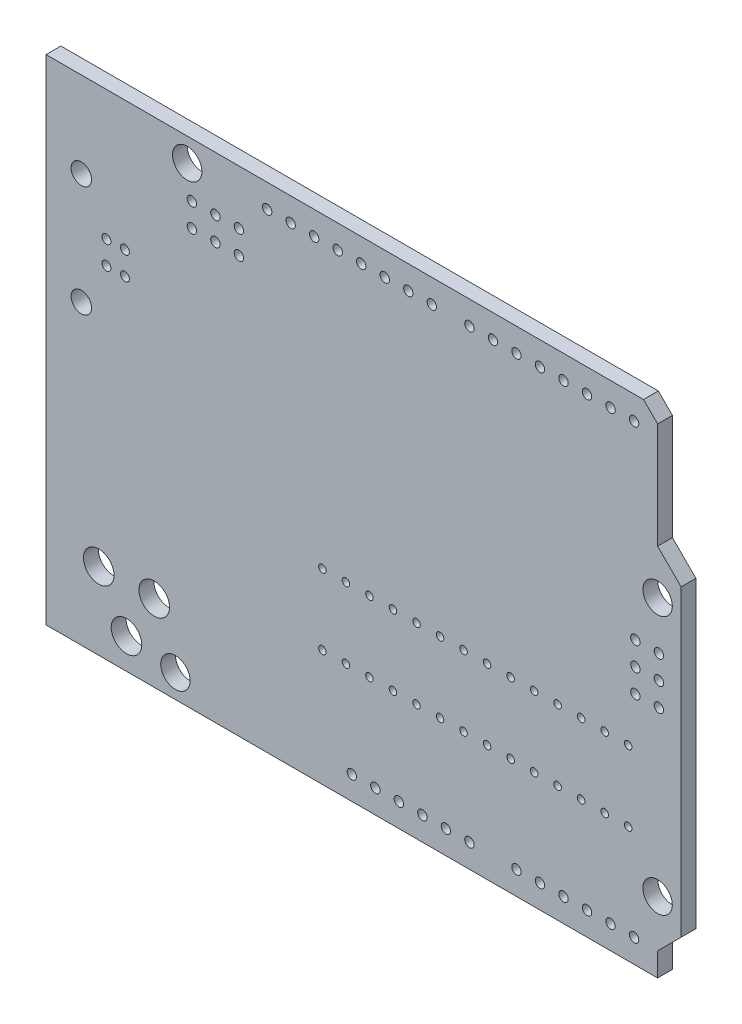
SolidWorks part; units mm, degrees
ref_plane "Front" through (0, 0, 0) normal (0, 0, 1) x (1, 0, 0)
ref_plane "Top" through (0, 0, 0) normal (0, 1, 0) x (1, 0, 0)
ref_plane "Right" through (0, 0, 0) normal (1, 0, 0) x (0, 0, -1)
sketch "Sketch1" plane through (0, 0, 0) normal (0, 0, 1) x (1, 0, 0)
  line L0 (-34.2899, 0) -> (34.2899, 0) construction
  line L1 (0, 0) -> (0, 7.605) construction
  line L2 (31.7499, 13.716) -> (31.7499, 25.146) construction
  line L3 (-34.2899, -26.67) -> (-34.2899, 26.67) construction
  line L4 (-34.2899, -26.67) -> (31.7499, -26.67) construction
  line L5 (31.7499, -26.67) -> (31.7499, -24.13) construction
  line L6 (31.7499, -24.13) -> (34.2899, -21.59) construction
  line L7 (34.2899, -21.59) -> (34.2899, 11.176) construction
  line L8 (31.7499, 13.716) -> (34.2899, 11.176) construction
  line L9 (30.2259, 26.67) -> (31.7499, 25.146) construction
  line L10 (-34.2899, 26.67) -> (30.2259, 26.67) construction
  arc A0 (-21.12, -24.13) -> (-19.5201, -24.13) centre (-20.3201, -24.13) ccw construction
  arc A1 (-19.5201, -24.13) -> (-21.12, -24.13) centre (-20.3201, -24.13) ccw construction
  arc A2 (-19.85, 24.13) -> (-18.2501, 24.13) centre (-19.0501, 24.13) ccw construction
  arc A3 (-18.2501, 24.13) -> (-19.85, 24.13) centre (-19.0501, 24.13) ccw construction
  arc A4 (30.95, -19.05) -> (32.5499, -19.05) centre (31.7499, -19.05) ccw construction
  arc A5 (32.5499, -19.05) -> (30.95, -19.05) centre (31.7499, -19.05) ccw construction
  arc A6 (30.95, 8.89) -> (32.5499, 8.89) centre (31.7499, 8.89) ccw construction
  arc A7 (32.5499, 8.89) -> (30.95, 8.89) centre (31.7499, 8.89) ccw construction
  arc A8 (28.3717, -14.097) -> (28.7781, -14.097) centre (28.5749, -14.097) ccw construction
  arc A9 (28.7781, -14.097) -> (28.3717, -14.097) centre (28.5749, -14.097) ccw construction
  arc A10 (25.8317, -14.097) -> (26.2381, -14.097) centre (26.0349, -14.097) ccw construction
  arc A11 (26.2381, -14.097) -> (25.8317, -14.097) centre (26.0349, -14.097) ccw construction
  arc A12 (23.2917, -14.097) -> (23.6981, -14.097) centre (23.4949, -14.097) ccw construction
  arc A13 (23.6981, -14.097) -> (23.2917, -14.097) centre (23.4949, -14.097) ccw construction
  arc A14 (20.7517, -14.097) -> (21.1581, -14.097) centre (20.9549, -14.097) ccw construction
  arc A15 (21.1581, -14.097) -> (20.7517, -14.097) centre (20.9549, -14.097) ccw construction
  arc A16 (18.2117, -14.097) -> (18.6181, -14.097) centre (18.4149, -14.097) ccw construction
  arc A17 (18.6181, -14.097) -> (18.2117, -14.097) centre (18.4149, -14.097) ccw construction
  arc A18 (15.6717, -14.097) -> (16.0781, -14.097) centre (15.8749, -14.097) ccw construction
  arc A19 (16.0781, -14.097) -> (15.6717, -14.097) centre (15.8749, -14.097) ccw construction
  arc A20 (13.1317, -14.097) -> (13.5381, -14.097) centre (13.3349, -14.097) ccw construction
  arc A21 (13.5381, -14.097) -> (13.1317, -14.097) centre (13.3349, -14.097) ccw construction
  arc A22 (10.5917, -14.097) -> (10.9981, -14.097) centre (10.7949, -14.097) ccw construction
  arc A23 (10.9981, -14.097) -> (10.5917, -14.097) centre (10.7949, -14.097) ccw construction
  arc A24 (8.0517, -14.097) -> (8.4581, -14.097) centre (8.2549, -14.097) ccw construction
  arc A25 (8.4581, -14.097) -> (8.0517, -14.097) centre (8.2549, -14.097) ccw construction
  arc A26 (5.5117, -14.097) -> (5.9181, -14.097) centre (5.7149, -14.097) ccw construction
  arc A27 (5.9181, -14.097) -> (5.5117, -14.097) centre (5.7149, -14.097) ccw construction
  arc A28 (2.9717, -14.097) -> (3.3781, -14.097) centre (3.1749, -14.097) ccw construction
  arc A29 (3.3781, -14.097) -> (2.9717, -14.097) centre (3.1749, -14.097) ccw construction
  arc A30 (0.4317, -14.097) -> (0.8381, -14.097) centre (0.6349, -14.097) ccw construction
  arc A31 (0.8381, -14.097) -> (0.4317, -14.097) centre (0.6349, -14.097) ccw construction
  arc A32 (-2.1083, -14.097) -> (-1.7019, -14.097) centre (-1.9051, -14.097) ccw construction
  arc A33 (-1.7019, -14.097) -> (-2.1083, -14.097) centre (-1.9051, -14.097) ccw construction
  arc A34 (-4.6483, -14.097) -> (-4.2419, -14.097) centre (-4.4451, -14.097) ccw construction
  arc A35 (-4.2419, -14.097) -> (-4.6483, -14.097) centre (-4.4451, -14.097) ccw construction
  arc A36 (-4.6483, -6.477) -> (-4.2419, -6.477) centre (-4.4451, -6.477) ccw construction
  arc A37 (-4.2419, -6.477) -> (-4.6483, -6.477) centre (-4.4451, -6.477) ccw construction
  arc A38 (-2.1083, -6.477) -> (-1.7019, -6.477) centre (-1.9051, -6.477) ccw construction
  arc A39 (-1.7019, -6.477) -> (-2.1083, -6.477) centre (-1.9051, -6.477) ccw construction
  arc A40 (0.4317, -6.477) -> (0.8381, -6.477) centre (0.6349, -6.477) ccw construction
  arc A41 (0.8381, -6.477) -> (0.4317, -6.477) centre (0.6349, -6.477) ccw construction
  arc A42 (2.9717, -6.477) -> (3.3781, -6.477) centre (3.1749, -6.477) ccw construction
  arc A43 (3.3781, -6.477) -> (2.9717, -6.477) centre (3.1749, -6.477) ccw construction
  arc A44 (5.5117, -6.477) -> (5.9181, -6.477) centre (5.7149, -6.477) ccw construction
  arc A45 (5.9181, -6.477) -> (5.5117, -6.477) centre (5.7149, -6.477) ccw construction
  arc A46 (8.0517, -6.477) -> (8.4581, -6.477) centre (8.2549, -6.477) ccw construction
  arc A47 (8.4581, -6.477) -> (8.0517, -6.477) centre (8.2549, -6.477) ccw construction
  arc A48 (10.5917, -6.477) -> (10.9981, -6.477) centre (10.7949, -6.477) ccw construction
  arc A49 (10.9981, -6.477) -> (10.5917, -6.477) centre (10.7949, -6.477) ccw construction
  arc A50 (13.1317, -6.477) -> (13.5381, -6.477) centre (13.3349, -6.477) ccw construction
  arc A51 (13.5381, -6.477) -> (13.1317, -6.477) centre (13.3349, -6.477) ccw construction
  arc A52 (15.6717, -6.477) -> (16.0781, -6.477) centre (15.8749, -6.477) ccw construction
  arc A53 (16.0781, -6.477) -> (15.6717, -6.477) centre (15.8749, -6.477) ccw construction
  arc A54 (18.2117, -6.477) -> (18.6181, -6.477) centre (18.4149, -6.477) ccw construction
  arc A55 (18.6181, -6.477) -> (18.2117, -6.477) centre (18.4149, -6.477) ccw construction
  arc A56 (20.7517, -6.477) -> (21.1581, -6.477) centre (20.9549, -6.477) ccw construction
  arc A57 (21.1581, -6.477) -> (20.7517, -6.477) centre (20.9549, -6.477) ccw construction
  arc A58 (23.2917, -6.477) -> (23.6981, -6.477) centre (23.4949, -6.477) ccw construction
  arc A59 (23.6981, -6.477) -> (23.2917, -6.477) centre (23.4949, -6.477) ccw construction
  arc A60 (25.8317, -6.477) -> (26.2381, -6.477) centre (26.0349, -6.477) ccw construction
  arc A61 (26.2381, -6.477) -> (25.8317, -6.477) centre (26.0349, -6.477) ccw construction
  arc A62 (28.3717, -6.477) -> (28.7781, -6.477) centre (28.5749, -6.477) ccw construction
  arc A63 (28.7781, -6.477) -> (28.3717, -6.477) centre (28.5749, -6.477) ccw construction
  arc A64 (-31.0299, 5.43) -> (-29.93, 5.43) centre (-30.4799, 5.43) ccw construction
  arc A65 (-29.93, 5.43) -> (-31.0299, 5.43) centre (-30.4799, 5.43) ccw construction
  arc A66 (-31.0299, 17.43) -> (-29.93, 17.43) centre (-30.4799, 17.43) ccw construction
  arc A67 (-29.93, 17.43) -> (-31.0299, 17.43) centre (-30.4799, 17.43) ccw construction
  arc A68 (-28.0074, 10.1801) -> (-27.5324, 10.1801) centre (-27.7699, 10.1801) ccw construction
  arc A69 (-27.5324, 10.1801) -> (-28.0074, 10.1801) centre (-27.7699, 10.1801) ccw construction
  arc A70 (-28.0074, 12.6799) -> (-27.5324, 12.6799) centre (-27.7699, 12.6799) ccw construction
  arc A71 (-27.5324, 12.6799) -> (-28.0074, 12.6799) centre (-27.7699, 12.6799) ccw construction
  arc A72 (-26.0075, 12.6799) -> (-25.5325, 12.6799) centre (-25.77, 12.6799) ccw construction
  arc A73 (-25.5325, 12.6799) -> (-26.0075, 12.6799) centre (-25.77, 12.6799) ccw construction
  arc A74 (-26.0075, 10.1801) -> (-25.5325, 10.1801) centre (-25.77, 10.1801) ccw construction
  arc A75 (-25.5325, 10.1801) -> (-26.0075, 10.1801) centre (-25.77, 10.1801) ccw construction
  arc A76 (-29.4258, -18.3642) -> (-27.7748, -18.3642) centre (-28.6003, -18.3642) ccw construction
  arc A77 (-27.7748, -18.3642) -> (-29.4258, -18.3642) centre (-28.6003, -18.3642) ccw construction
  arc A78 (-23.4316, -18.3642) -> (-21.7806, -18.3642) centre (-22.6061, -18.3642) ccw construction
  arc A79 (-21.7806, -18.3642) -> (-23.4316, -18.3642) centre (-22.6061, -18.3642) ccw construction
  arc A80 (-26.4286, -23.368) -> (-24.7776, -23.368) centre (-25.6031, -23.368) ccw construction
  arc A81 (-24.7776, -23.368) -> (-26.4286, -23.368) centre (-25.6031, -23.368) ccw construction
  arc A82 (8.7375, -2.54) -> (9.0423, -2.54) centre (8.8899, -2.54) ccw construction
  arc A83 (9.0423, -2.54) -> (8.7375, -2.54) centre (8.8899, -2.54) ccw construction
  arc A84 (3.6575, -2.54) -> (3.9623, -2.54) centre (3.8099, -2.54) ccw construction
  arc A85 (3.9623, -2.54) -> (3.6575, -2.54) centre (3.8099, -2.54) ccw construction
  arc A86 (-20.4725, 3.81) -> (-20.1677, 3.81) centre (-20.3201, 3.81) ccw construction
  arc A87 (-20.1677, 3.81) -> (-20.4725, 3.81) centre (-20.3201, 3.81) ccw construction
  arc A88 (-15.3925, 3.81) -> (-15.0877, 3.81) centre (-15.2401, 3.81) ccw construction
  arc A89 (-15.0877, 3.81) -> (-15.3925, 3.81) centre (-15.2401, 3.81) ccw construction
  arc A90 (11.1759, -24.13) -> (11.6839, -24.13) centre (11.4299, -24.13) ccw construction
  arc A91 (11.6839, -24.13) -> (11.1759, -24.13) centre (11.4299, -24.13) ccw construction
  arc A92 (8.6359, -24.13) -> (9.1439, -24.13) centre (8.8899, -24.13) ccw construction
  arc A93 (9.1439, -24.13) -> (8.6359, -24.13) centre (8.8899, -24.13) ccw construction
  arc A94 (6.0959, -24.13) -> (6.6039, -24.13) centre (6.3499, -24.13) ccw construction
  arc A95 (6.6039, -24.13) -> (6.0959, -24.13) centre (6.3499, -24.13) ccw construction
  arc A96 (3.5559, -24.13) -> (4.0639, -24.13) centre (3.8099, -24.13) ccw construction
  arc A97 (4.0639, -24.13) -> (3.5559, -24.13) centre (3.8099, -24.13) ccw construction
  arc A98 (1.0159, -24.13) -> (1.5239, -24.13) centre (1.2699, -24.13) ccw construction
  arc A99 (1.5239, -24.13) -> (1.0159, -24.13) centre (1.2699, -24.13) ccw construction
  arc A100 (-1.5241, -24.13) -> (-1.0161, -24.13) centre (-1.2701, -24.13) ccw construction
  arc A101 (-1.0161, -24.13) -> (-1.5241, -24.13) centre (-1.2701, -24.13) ccw construction
  arc A102 (11.1759, 24.13) -> (11.6839, 24.13) centre (11.4299, 24.13) ccw construction
  arc A103 (11.6839, 24.13) -> (11.1759, 24.13) centre (11.4299, 24.13) ccw construction
  arc A104 (13.7159, 24.13) -> (14.2239, 24.13) centre (13.9699, 24.13) ccw construction
  arc A105 (14.2239, 24.13) -> (13.7159, 24.13) centre (13.9699, 24.13) ccw construction
  arc A106 (16.2559, 24.13) -> (16.7639, 24.13) centre (16.5099, 24.13) ccw construction
  arc A107 (16.7639, 24.13) -> (16.2559, 24.13) centre (16.5099, 24.13) ccw construction
  arc A108 (18.7959, 24.13) -> (19.3039, 24.13) centre (19.0499, 24.13) ccw construction
  arc A109 (19.3039, 24.13) -> (18.7959, 24.13) centre (19.0499, 24.13) ccw construction
  arc A110 (21.3359, 24.13) -> (21.8439, 24.13) centre (21.5899, 24.13) ccw construction
  arc A111 (21.8439, 24.13) -> (21.3359, 24.13) centre (21.5899, 24.13) ccw construction
  arc A112 (23.8759, 24.13) -> (24.3839, 24.13) centre (24.1299, 24.13) ccw construction
  arc A113 (24.3839, 24.13) -> (23.8759, 24.13) centre (24.1299, 24.13) ccw construction
  arc A114 (26.4159, 24.13) -> (26.9239, 24.13) centre (26.6699, 24.13) ccw construction
  arc A115 (26.9239, 24.13) -> (26.4159, 24.13) centre (26.6699, 24.13) ccw construction
  arc A116 (28.9559, 24.13) -> (29.4639, 24.13) centre (29.2099, 24.13) ccw construction
  arc A117 (29.4639, 24.13) -> (28.9559, 24.13) centre (29.2099, 24.13) ccw construction
  arc A118 (-10.6681, 24.13) -> (-10.1601, 24.13) centre (-10.4141, 24.13) ccw construction
  arc A119 (-10.1601, 24.13) -> (-10.6681, 24.13) centre (-10.4141, 24.13) ccw construction
  arc A120 (-8.1281, 24.13) -> (-7.6201, 24.13) centre (-7.8741, 24.13) ccw construction
  arc A121 (-7.6201, 24.13) -> (-8.1281, 24.13) centre (-7.8741, 24.13) ccw construction
  arc A122 (-5.5881, 24.13) -> (-5.0801, 24.13) centre (-5.3341, 24.13) ccw construction
  arc A123 (-5.0801, 24.13) -> (-5.5881, 24.13) centre (-5.3341, 24.13) ccw construction
  arc A124 (-3.0481, 24.13) -> (-2.5401, 24.13) centre (-2.7941, 24.13) ccw construction
  arc A125 (-2.5401, 24.13) -> (-3.0481, 24.13) centre (-2.7941, 24.13) ccw construction
  arc A126 (-0.5081, 24.13) -> (-0.0001, 24.13) centre (-0.2541, 24.13) ccw construction
  arc A127 (-0.0001, 24.13) -> (-0.5081, 24.13) centre (-0.2541, 24.13) ccw construction
  arc A128 (2.0319, 24.13) -> (2.5399, 24.13) centre (2.2859, 24.13) ccw construction
  arc A129 (2.5399, 24.13) -> (2.0319, 24.13) centre (2.2859, 24.13) ccw construction
  arc A130 (4.5719, 24.13) -> (5.0799, 24.13) centre (4.8259, 24.13) ccw construction
  arc A131 (5.0799, 24.13) -> (4.5719, 24.13) centre (4.8259, 24.13) ccw construction
  arc A132 (7.1119, 24.13) -> (7.6199, 24.13) centre (7.3659, 24.13) ccw construction
  arc A133 (7.6199, 24.13) -> (7.1119, 24.13) centre (7.3659, 24.13) ccw construction
  arc A134 (-18.7961, 18.288) -> (-18.2881, 18.288) centre (-18.5421, 18.288) ccw construction
  arc A135 (-18.2881, 18.288) -> (-18.7961, 18.288) centre (-18.5421, 18.288) ccw construction
  arc A136 (-18.7961, 20.828) -> (-18.2881, 20.828) centre (-18.5421, 20.828) ccw construction
  arc A137 (-18.2881, 20.828) -> (-18.7961, 20.828) centre (-18.5421, 20.828) ccw construction
  arc A138 (-16.2561, 18.288) -> (-15.7481, 18.288) centre (-16.0021, 18.288) ccw construction
  arc A139 (-15.7481, 18.288) -> (-16.2561, 18.288) centre (-16.0021, 18.288) ccw construction
  arc A140 (-16.2561, 20.828) -> (-15.7481, 20.828) centre (-16.0021, 20.828) ccw construction
  arc A141 (-15.7481, 20.828) -> (-16.2561, 20.828) centre (-16.0021, 20.828) ccw construction
  arc A142 (-13.7161, 18.288) -> (-13.2081, 18.288) centre (-13.4621, 18.288) ccw construction
  arc A143 (-13.2081, 18.288) -> (-13.7161, 18.288) centre (-13.4621, 18.288) ccw construction
  arc A144 (-13.7161, 20.828) -> (-13.2081, 20.828) centre (-13.4621, 20.828) ccw construction
  arc A145 (-13.2081, 20.828) -> (-13.7161, 20.828) centre (-13.4621, 20.828) ccw construction
  arc A146 (31.6362, -1.32) -> (32.1442, -1.32) centre (31.8902, -1.32) ccw construction
  arc A147 (32.1442, -1.32) -> (31.6362, -1.32) centre (31.8902, -1.32) ccw construction
  arc A148 (29.0962, -1.32) -> (29.6042, -1.32) centre (29.3502, -1.32) ccw construction
  arc A149 (29.6042, -1.32) -> (29.0962, -1.32) centre (29.3502, -1.32) ccw construction
  arc A150 (31.6362, 1.22) -> (32.1442, 1.22) centre (31.8902, 1.22) ccw construction
  arc A151 (32.1442, 1.22) -> (31.6362, 1.22) centre (31.8902, 1.22) ccw construction
  arc A152 (29.0962, 1.22) -> (29.6042, 1.22) centre (29.3502, 1.22) ccw construction
  arc A153 (29.6042, 1.22) -> (29.0962, 1.22) centre (29.3502, 1.22) ccw construction
  arc A154 (31.6362, 3.76) -> (32.1442, 3.76) centre (31.8902, 3.76) ccw construction
  arc A155 (32.1442, 3.76) -> (31.6362, 3.76) centre (31.8902, 3.76) ccw construction
  arc A156 (29.0962, 3.76) -> (29.6042, 3.76) centre (29.3502, 3.76) ccw construction
  arc A157 (29.6042, 3.76) -> (29.0962, 3.76) centre (29.3502, 3.76) ccw construction
  arc A158 (28.9559, -24.13) -> (29.4639, -24.13) centre (29.2099, -24.13) ccw construction
  arc A159 (29.4639, -24.13) -> (28.9559, -24.13) centre (29.2099, -24.13) ccw construction
  arc A160 (26.4159, -24.13) -> (26.9239, -24.13) centre (26.6699, -24.13) ccw construction
  arc A161 (26.9239, -24.13) -> (26.4159, -24.13) centre (26.6699, -24.13) ccw construction
  arc A162 (23.8759, -24.13) -> (24.3839, -24.13) centre (24.1299, -24.13) ccw construction
  arc A163 (24.3839, -24.13) -> (23.8759, -24.13) centre (24.1299, -24.13) ccw construction
  arc A164 (21.3359, -24.13) -> (21.8439, -24.13) centre (21.5899, -24.13) ccw construction
  arc A165 (21.8439, -24.13) -> (21.3359, -24.13) centre (21.5899, -24.13) ccw construction
  arc A166 (18.7959, -24.13) -> (19.3039, -24.13) centre (19.0499, -24.13) ccw construction
  arc A167 (19.3039, -24.13) -> (18.7959, -24.13) centre (19.0499, -24.13) ccw construction
  arc A168 (16.2559, -24.13) -> (16.7639, -24.13) centre (16.5099, -24.13) ccw construction
  arc A169 (16.7639, -24.13) -> (16.2559, -24.13) centre (16.5099, -24.13) ccw construction
sketch "Sketch2" plane through (0, 0, 0) normal (0, 0, 1) x (1, 0, 0)
  line L0 (-34.2899, 26.67) -> (30.2259, 26.67) construction
  line L1 (-34.2899, -26.67) -> (-34.2899, 26.67) construction
  line L2 (-34.2899, -26.67) -> (31.7499, -26.67) construction
  line L3 (31.7499, -26.67) -> (31.7499, -24.13) construction
  line L4 (31.7499, -24.13) -> (34.2899, -21.59) construction
  line L5 (34.2899, -21.59) -> (34.2899, 11.176) construction
  line L6 (31.7499, 13.716) -> (34.2899, 11.176) construction
  line L7 (31.7499, 13.716) -> (31.7499, 25.146) construction
  line L8 (30.2259, 26.67) -> (31.7499, 25.146) construction
  line L9 (-34.2899, 26.67) -> (30.2259, 26.67)
  line L10 (-34.2899, -26.67) -> (-34.2899, 26.67)
  line L11 (-34.2899, -26.67) -> (31.7499, -26.67)
  line L12 (31.7499, -26.67) -> (31.7499, -24.13)
  line L13 (31.7499, -24.13) -> (34.2899, -21.59)
  line L14 (34.2899, -21.59) -> (34.2899, 11.176)
  line L15 (31.7499, 13.716) -> (34.2899, 11.176)
  line L16 (31.7499, 13.716) -> (31.7499, 25.146)
  line L17 (30.2259, 26.67) -> (31.7499, 25.146)
extrude "Boss-Extrude1" add sketch "Sketch2" against normal blind 1.6002
sketch "Sketch3" plane through (0, 0, 0) normal (0, 0, 1) x (1, 0, 0)
  circle A0 centre (-30.4799, 17.43) radius 1.1049
  circle A1 centre (-30.4799, 5.43) radius 1.1049
  circle A2 centre (-28.6003, -18.3642) radius 1.651
  circle A3 centre (-25.6031, -23.368) radius 1.651
  circle A4 centre (-22.6061, -18.3642) radius 1.651
  circle A5 centre (31.7499, -19.05) radius 1.5875
  circle A6 centre (31.7499, 8.89) radius 1.5875
  circle A7 centre (-19.0501, 24.13) radius 1.5875
  circle A8 centre (-25.77, 12.6799) radius 0.4826
  circle A9 centre (-27.7699, 12.6799) radius 0.4826
  circle A10 centre (-27.7699, 10.1801) radius 0.4826
  circle A11 centre (-25.77, 10.1801) radius 0.4826
  circle A12 centre (-20.3201, -24.13) radius 1.5875
  dimension "D1" = 3.175
  dimension "D2" = 3.175
  dimension "D3" = 3.175
  dimension "D4" = 3.302
  dimension "D5" = 3.302
  dimension "D6" = 3.302
  dimension "D7" = 2.2098
  dimension "D8" = 2.2098
  dimension "D9" = 0.9652
  dimension "D10" = 0.9652
  dimension "D11" = 0.9652
  dimension "D12" = 0.9652
  dimension "D13" = 3.175
extrude "Cut-Extrude1" cut sketch "Sketch3" against normal through all
sketch "Sketch4" plane through (0, 0, 0) normal (0, 0, 1) x (1, 0, 0)
  circle A0 centre (29.2099, 24.13) radius 0.508
  circle A1 centre (26.6699, 24.13) radius 0.508
  circle A2 centre (24.1299, 24.13) radius 0.508
  circle A3 centre (21.5899, 24.13) radius 0.508
  circle A4 centre (19.0499, 24.13) radius 0.508
  circle A5 centre (16.5099, 24.13) radius 0.508
  circle A6 centre (13.9699, 24.13) radius 0.508
  circle A7 centre (11.4299, 24.13) radius 0.508
  circle A8 centre (7.3659, 24.13) radius 0.508
  circle A9 centre (4.8259, 24.13) radius 0.508
  circle A10 centre (2.2859, 24.13) radius 0.508
  circle A11 centre (-0.2541, 24.13) radius 0.508
  circle A12 centre (-2.7941, 24.13) radius 0.508
  circle A13 centre (-5.3341, 24.13) radius 0.508
  circle A14 centre (-7.8741, 24.13) radius 0.508
  circle A15 centre (-10.4141, 24.13) radius 0.508
  circle A16 centre (28.5749, -6.477) radius 0.4064
  circle A17 centre (26.0349, -6.477) radius 0.4064
  circle A18 centre (23.4949, -6.477) radius 0.4064
  circle A19 centre (20.9549, -6.477) radius 0.4064
  circle A20 centre (18.4149, -6.477) radius 0.4064
  circle A21 centre (15.8749, -6.477) radius 0.4064
  circle A22 centre (13.3349, -6.477) radius 0.4064
  circle A23 centre (10.7949, -6.477) radius 0.4064
  circle A24 centre (8.2549, -6.477) radius 0.4064
  circle A25 centre (5.7149, -6.477) radius 0.4064
  circle A26 centre (3.1749, -6.477) radius 0.4064
  circle A27 centre (0.6349, -6.477) radius 0.4064
  circle A28 centre (-1.9051, -6.477) radius 0.4064
  circle A29 centre (-4.4451, -6.477) radius 0.4064
  circle A30 centre (28.5749, -14.097) radius 0.4064
  circle A31 centre (26.0349, -14.097) radius 0.4064
  circle A32 centre (23.4949, -14.097) radius 0.4064
  circle A33 centre (20.9549, -14.097) radius 0.4064
  circle A34 centre (18.4149, -14.097) radius 0.4064
  circle A35 centre (15.8749, -14.097) radius 0.4064
  circle A36 centre (13.3349, -14.097) radius 0.4064
  circle A37 centre (10.7949, -14.097) radius 0.4064
  circle A38 centre (8.2549, -14.097) radius 0.4064
  circle A39 centre (5.7149, -14.097) radius 0.4064
  circle A40 centre (3.1749, -14.097) radius 0.4064
  circle A41 centre (0.6349, -14.097) radius 0.4064
  circle A42 centre (-1.9051, -14.097) radius 0.4064
  circle A43 centre (-4.4451, -14.097) radius 0.4064
  circle A44 centre (29.2099, -24.13) radius 0.508
  circle A45 centre (11.4299, -24.13) radius 0.508
  circle A46 centre (26.6699, -24.13) radius 0.508
  circle A47 centre (8.8899, -24.13) radius 0.508
  circle A48 centre (24.1299, -24.13) radius 0.508
  circle A49 centre (6.3499, -24.13) radius 0.508
  circle A50 centre (21.5899, -24.13) radius 0.508
  circle A51 centre (3.8099, -24.13) radius 0.508
  circle A52 centre (19.0499, -24.13) radius 0.508
  circle A53 centre (1.2699, -24.13) radius 0.508
  circle A54 centre (16.5099, -24.13) radius 0.508
  circle A55 centre (-1.2701, -24.13) radius 0.508
  circle A56 centre (-13.4621, 20.828) radius 0.508
  circle A57 centre (-13.4621, 18.288) radius 0.508
  circle A58 centre (-16.0021, 18.288) radius 0.508
  circle A59 centre (-16.0021, 20.828) radius 0.508
  circle A60 centre (-18.5421, 18.288) radius 0.508
  circle A61 centre (-18.5421, 20.828) radius 0.508
  circle A62 centre (31.8902, -1.32) radius 0.508
  circle A63 centre (29.3502, -1.32) radius 0.508
  circle A64 centre (29.3502, 1.22) radius 0.508
  circle A65 centre (31.8902, 1.22) radius 0.508
  circle A66 centre (29.3502, 3.76) radius 0.508
  circle A67 centre (31.8902, 3.76) radius 0.508
  dimension "D1" = 1.016
  dimension "D3" = 1.016
  dimension "D5" = 0.8128
  dimension "D7" = 0.8128
  dimension "D9" = 1.016
  dimension "D10" = 1.016
  dimension "D12" = 1.016
  dimension "D13" = 1.016
  dimension "D15" = 1.016
  dimension "D16" = 1.016
  dimension "D2" = 8
  dimension "D4" = 8
  dimension "D6" = 14
  dimension "D8" = 14
  dimension "D11" = 6
  dimension "D14" = 3
  dimension "D17" = 3
extrude "Cut-Extrude2" cut sketch "Sketch4" against normal through all
